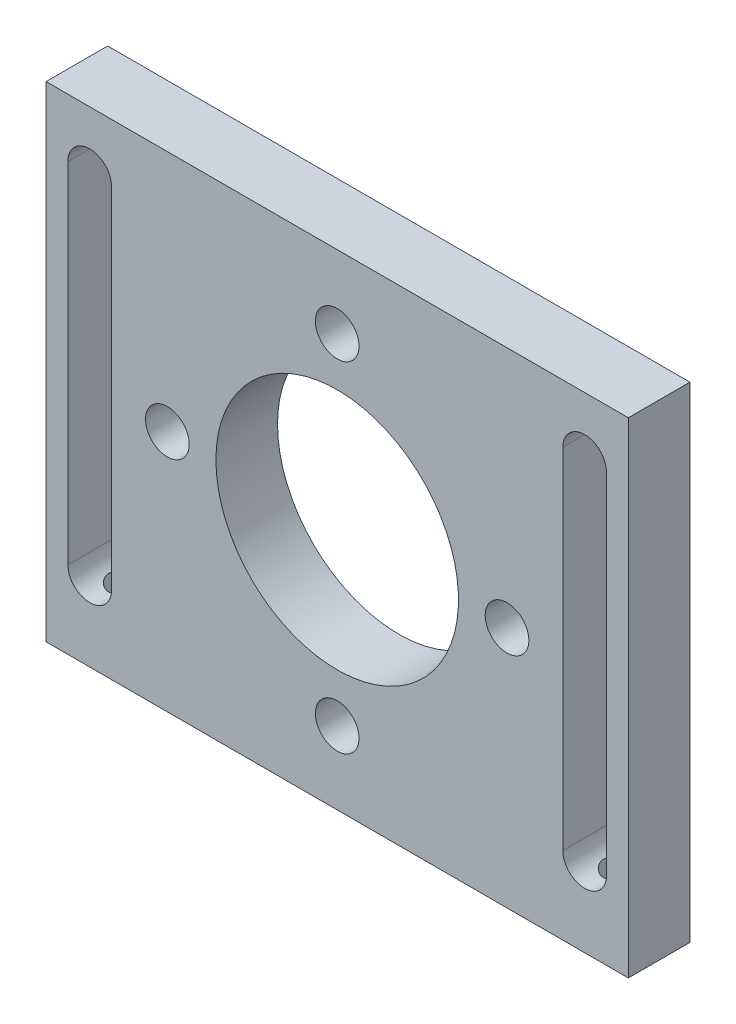
SolidWorks part; units mm, degrees
ref_plane "Front Plane" through (0, 0, 0) normal (0, 0, 1) x (1, 0, 0)
ref_plane "Top Plane" through (0, 0, 0) normal (0, 1, 0) x (1, 0, 0)
ref_plane "Right Plane" through (0, 0, 0) normal (1, 0, 0) x (0, 0, -1)
ref_plane "Plane1" through (0, 0, 0) normal (0, 0, -1) x (-1, 0, 0)
sketch "Sketch1" plane through (0, 0, 0) normal (0, 0, -1) x (-1, 0, 0)
  line L0 (-30, -25) -> (30, -25)
  line L1 (30, -25) -> (30, 25)
  line L2 (30, 25) -> (-30, 25)
  line L3 (-30, 25) -> (-30, -25)
extrude "Boss-Extrude1" add sketch "Sketch1" against normal blind 6.35
sketch "Sketch2" plane through (0, 0, 0) normal (0, 0, -1) x (-1, 0, 0)
  line L0 (23.25, 19) -> (23.25, -17)
  line L1 (27.75, -17) -> (27.75, 19)
  arc A0 (23.25, -17) -> (27.75, -17) centre (25.5, -17) ccw
  arc A1 (27.75, 19) -> (23.25, 19) centre (25.5, 19) ccw
extrude "Cut-Extrude1" cut sketch "Sketch2" against normal through all
sketch "Sketch3" plane through (0, 0, 6.35) normal (0, 0, 1) x (1, 0, 0)
  line L0 (27.75, -17) -> (27.75, 19)
  line L1 (23.25, 19) -> (23.25, -17)
  arc A0 (27.75, 19) -> (23.25, 19) centre (25.5, 19) ccw
  arc A1 (23.25, -17) -> (27.75, -17) centre (25.5, -17) ccw
extrude "Cut-Extrude2" cut sketch "Sketch3" against normal through all
hole_wizard "Hole1" positions "Sketch5" profile "Sketch4" legacy
sketch "Sketch5" plane through (0, 0, 0) normal (0, 0, -1) x (-1, 0, 0)
  point P0 (0, 0)
sketch "Sketch4" plane through (0, 0, 0) normal (1, 0, 0) x (0, 1, 0)
  line L0 (0, 0) -> (0, 6.35)
  line L1 (0, 6.35) -> (12.5, 6.35)
  line L2 (12.5, 6.35) -> (12.5, 0)
  line L3 (12.5, 0) -> (0, 0)
  line L4 (0, 110) -> (0, -10) construction
  dimension "Diameter" = 25
  dimension "Depth" = 6.35
hole_wizard "#8 Clearance Hole1" positions "Sketch7" profile "Sketch6" hole size "#8" standard "ANSI Inch"
sketch "Sketch7" plane through (0, 0, 0) normal (0, 0, -1) x (-1, 0, 0)
  point P0 (0, 17.5)
  point P1 (17.5, 0)
  point P2 (0, -17.5)
  point P3 (-17.5, 0)
sketch "Sketch6" plane through (0, 17.5, 0) normal (1, 0, 0) x (0, 1, 0)
  line L0 (0, 0) -> (0, 6.35)
  line L1 (0, 6.35) -> (2.25, 6.35)
  line L2 (2.25, 6.35) -> (2.25, 0)
  line L5 (2.25, 0) -> (0, 0)
  line L11 (0, -6.35) -> (0, 107.95) construction
  dimension "Thru Hole Dia." = 4.5
  dimension "Thru Hole Depth" = 6.35
hole_wizard "#2 Clearance Hole1" positions "Sketch9" profile "Sketch8" hole size "#2" standard "ANSI Inch"
sketch "Sketch9" plane through (0, -25, 0) normal (0, -1, 0) x (-1, 0, 0)
  point P0 (-25.5, -3.175)
  point P1 (25.5, -3.175)
sketch "Sketch8" plane through (25.5, -25, 3.175) normal (1, 0, 0) x (0, 0, -1)
  line L0 (0, 0) -> (0, 5.75)
  line L1 (0, 5.75) -> (1.25, 5.75)
  line L2 (1.25, 5.75) -> (1.25, 0)
  line L5 (1.25, 0) -> (0, 0)
  line L11 (0, -6.35) -> (0, 107.95) construction
  dimension "Thru Hole Dia." = 2.5
  dimension "Thru Hole Depth" = 5.75
chamfer "Chamfer1" distance 2.45 angle 45 4 edges at (15.25, 0, 0) (-2.25, -17.5, 0) (-2.25, 17.5, 0) (-19.75, 0, 0)
